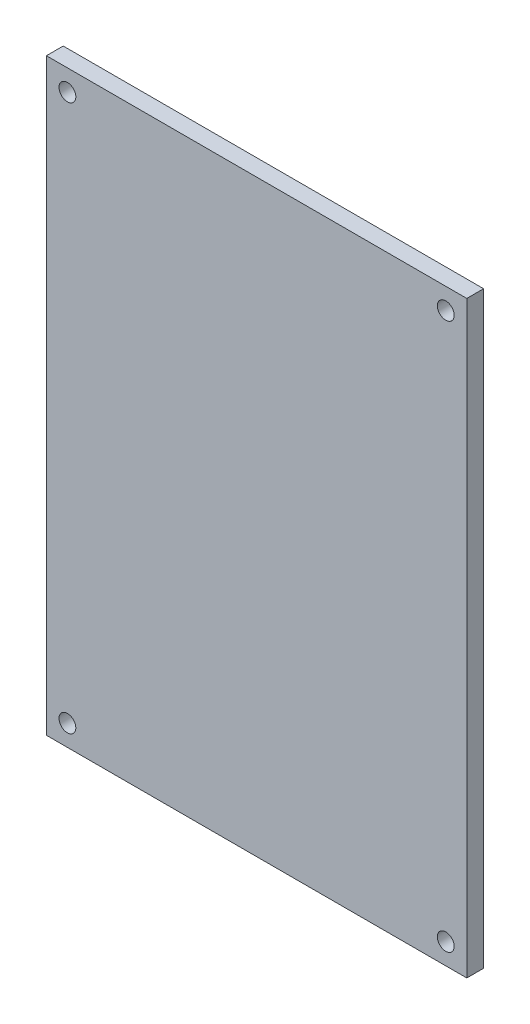
SolidWorks part; units mm, degrees
ref_plane "前视基准面" through (0, 0, 0) normal (0, 0, 1) x (1, 0, 0)
ref_plane "上视基准面" through (0, 0, 0) normal (0, 1, 0) x (1, 0, 0)
ref_plane "右视基准面" through (0, 0, 0) normal (1, 0, 0) x (0, 0, -1)
sketch "草图1" plane through (0, 0, 0) normal (0, 0, 1) x (1, 0, 0)
  line L0 (0, 0) -> (0, 10) construction
  line L1 (-25, 35) -> (25, 35)
  line L2 (-25, 35) -> (-25, -35)
  line L3 (-25, -35) -> (25, -35)
  line L4 (25, 35) -> (25, -35)
  line L5 (-25, 35) -> (25, -35) construction
  line L6 (-25, -35) -> (25, 35) construction
  line L7 (0, 0) -> (10, 0) construction
  line L8 (-25, 35) -> (-25, 32.5) construction
  line L9 (-25, 32.5) -> (-22.5, 32.5) construction
  circle A0 centre (-22.5, 32.5) radius 1
  circle A1 centre (22.5, 32.5) radius 1
  circle A2 centre (22.5, -32.5) radius 1
  circle A3 centre (-22.5, -32.5) radius 1
  point P0 (0, 0)
  dimension "D1" = 50
  dimension "D3" = 2
  dimension "D5" = 2.5
  dimension "D2" = 70
  dimension "D4" = 2.5
extrude "凸台-拉伸1" add sketch "草图1" along normal blind 2
sketch "草图2" plane through (0, 0, 2) normal (0, 0, 1) x (1, 0, 0)
  line L0 (25, -35) -> (25, -5.7) construction
  line L1 (25, -35) -> (25, 35) construction
  line L2 (25, -5.7) -> (11, -5.7) construction
  line L3 (0, 0) -> (0, 10) construction
  line L4 (0, 0) -> (10, 0) construction
  line L5 (-25, -5.7) -> (-11, -5.7) construction
  line L6 (-11, -5.7) -> (11, -5.7)
  line L7 (11, -5.7) -> (11, 22.3)
  line L8 (11, 22.3) -> (-11, 22.3)
  line L9 (-11, 22.3) -> (-11, -5.7)
  dimension "D1" = 29.3
  dimension "D2" = 14
  dimension "D3" = 28
